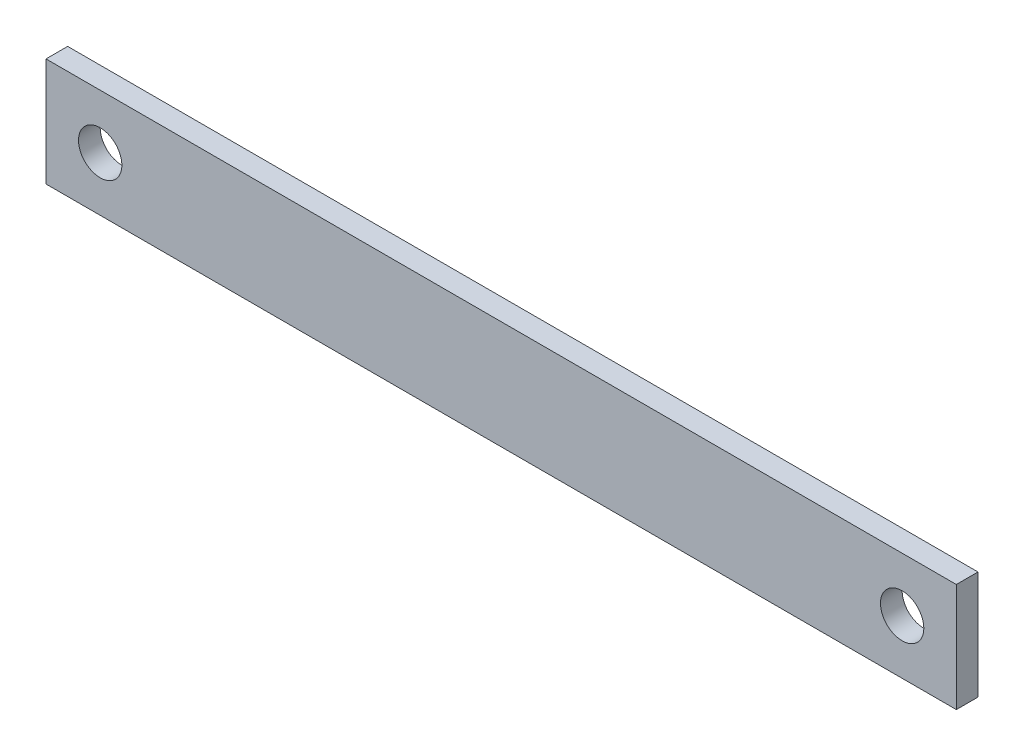
SolidWorks part; units mm, degrees
material "ABS"
ref_plane "Front Plane" through (0, 0, 0) normal (0, 0, 1) x (1, 0, 0)
ref_plane "Top Plane" through (0, 0, 0) normal (0, 1, 0) x (1, 0, 0)
ref_plane "Right Plane" through (0, 0, 0) normal (1, 0, 0) x (0, 0, -1)
sketch "Sketch1" plane through (0, 0, 0) normal (0, 0, 1) x (1, 0, 0)
  line L1 (-63.8591, -4.1686) -> (20.1409, -4.1686)
  line L2 (-63.8591, -4.1686) -> (-63.8591, 5.8314)
  line L3 (-63.8591, 5.8314) -> (20.1409, 5.8314)
  line L4 (20.1409, -4.1686) -> (20.1409, 5.8314)
  dimension "D1" = 10
  dimension "D2" = 84
extrude "Boss-Extrude1" add sketch "Sketch1" along normal blind 2 contours L3 L4 L1 L2
sketch "Sketch2" plane through (0, 0, 2) normal (0, 0, 1) x (1, 0, 0)
  line L0 (20.1409, -4.1686) -> (20.1409, 5.8314) construction
  line L1 (-63.8591, 5.8314) -> (20.1409, 5.8314) construction
  line L2 (-63.8591, -4.1686) -> (-63.8591, 5.8314) construction
  circle A0 centre (-58.8591, 0.8314) radius 2
  circle A1 centre (15.1409, 0.8314) radius 2
  dimension "D1" = 4
  dimension "D2" = 4
  dimension "D3" = 5
  dimension "D4" = 5
  dimension "D5" = 5
  dimension "D6" = 5
extrude "Cut-Extrude1" cut sketch "Sketch2" against normal blind 10
